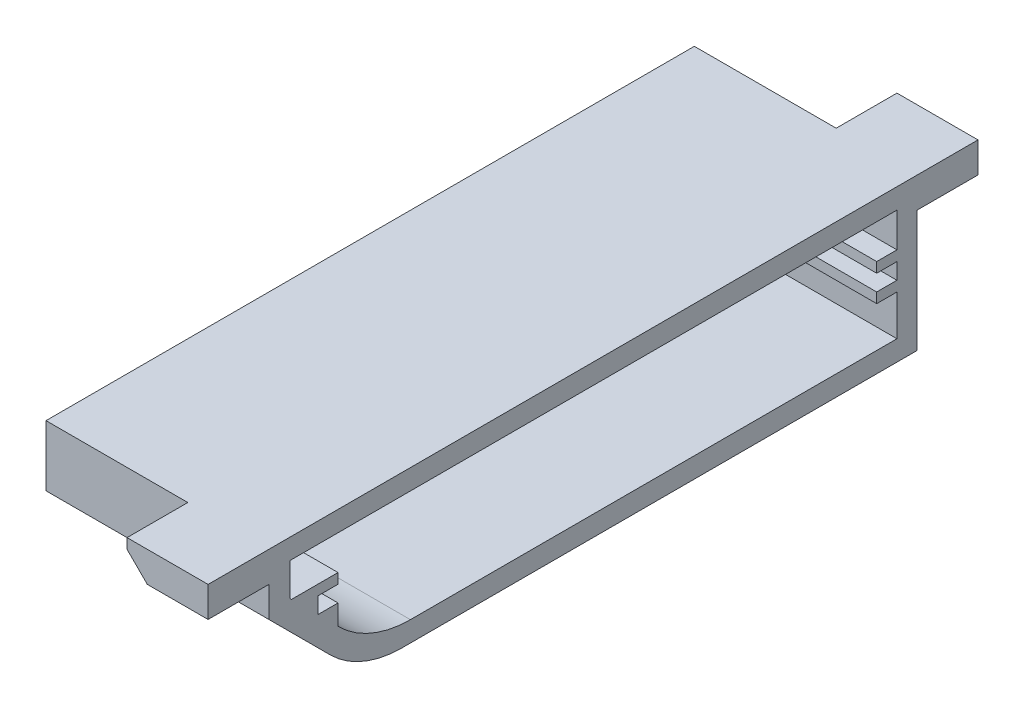
SolidWorks part; units mm, degrees
ref_plane "前视基准面" through (0, 0, 0) normal (0, 0, 1) x (1, 0, 0)
ref_plane "上视基准面" through (0, 0, 0) normal (0, 1, 0) x (1, 0, 0)
ref_plane "右视基准面" through (0, 0, 0) normal (1, 0, 0) x (0, 0, -1)
sketch "草图1" plane through (0, 0, 0) normal (0, 0, 1) x (1, 0, 0)
  line L0 (0, 0) -> (22, 0)
  line L1 (0, 0) -> (0, 15)
  line L2 (0, 15) -> (22, 15)
  line L3 (22, 15) -> (22, 0)
extrude "凸台-拉伸1" add sketch "草图1" along normal blind 2
sketch "草图2" plane through (0, 0, 0) normal (0, -1, 0) x (1, 0, 0)
  line L0 (0, 0) -> (0, 30)
  line L2 (22, 0) -> (22, 30)
  line L3 (22, 30) -> (0, 30)
  line L4 (0, 0) -> (22, 0)
extrude "凸台-拉伸2" add sketch "草图2" against normal blind 2
sketch "草图3" plane through (0, 0, 0) normal (-1, 0, 0) x (0, 0, 1)
  line L0 (0, 15) -> (64, 15)
  line L3 (0, 15) -> (0, 0) construction
  line L4 (0, 13) -> (0, 15)
  line L5 (64, 15) -> (64, 9)
  line L6 (64, 8) -> (64, 15) construction
  line L7 (30, 2) -> (53.4794, 2)
  line L8 (61.932, 10.4526) -> (61.932, 13)
  line L10 (30, 2) -> (30, 0)
  line L11 (61.932, 13) -> (0, 13)
  line L12 (30, 0) -> (55, 0)
  line L13 (64, 9) -> (55, 0)
  line L14 (60.9069, 8.7353) -> (60.9069, 8.7353)
  line L15 (60.9069, 8.7353) -> (60.9069, 8.7353)
  line L16 (60.9069, 8.7353) -> (60.9069, 8.7353)
  line L17 (60.9069, 8.7353) -> (60.9069, 8.7353)
  line L18 (60.9069, 8.7353) -> (60.9069, 8.7353)
  line L19 (60.9069, 8.7353) -> (55.1967, 3.0251)
  line L20 (55.1967, 3.0251) -> (55.1967, 3.0251)
  line L21 (55.1967, 3.0251) -> (55.1967, 3.0251)
  line L22 (55.1967, 3.0251) -> (55.1967, 3.0251)
  line L23 (60.9069, 8.7353) -> (61.932, 9.7604)
  line L24 (61.932, 9.7604) -> (61.932, 10.4526)
  line L25 (55.1967, 3.0251) -> (54.1716, 2)
  line L26 (54.1716, 2) -> (53.4794, 2)
  dimension "D1" = 2
extrude "凸台-拉伸3" add sketch "草图3" against normal blind 22
sketch "草图4" plane through (0, 0, 64) normal (0, 0, 1) x (1, 0, 0)
  line L1 (22, 15) -> (14, 15)
  line L2 (22, 15) -> (22, 12)
  line L3 (22, 12) -> (14, 12)
  line L4 (14, 15) -> (14, 12)
extrude "凸台-拉伸4" add sketch "草图4" along normal blind 6
sketch "草图5" plane through (0, 0, 0) normal (0, 0, -1) x (-1, 0, 0)
  line L1 (-22, 15) -> (-14, 15)
  line L2 (-22, 15) -> (-22, 12)
  line L3 (-22, 12) -> (-14, 12)
  line L4 (-14, 15) -> (-14, 12)
extrude "凸台-拉伸5" add sketch "草图5" along normal blind 6
chamfer "倒角1" distance 2 angle 45 2 edges at (14, 12, 67) (14, 12, -3)
sketch "草图6" plane through (0, 0, 0) normal (-1, 0, 0) x (0, 0, 1)
  line L0 (57.1716, 7) -> (59.1716, 7)
  line L1 (2, 13) -> (2, 2) construction
  line L2 (2, 6) -> (4, 6)
  line L3 (4, 6) -> (4, 7)
  line L4 (4, 7) -> (2, 7)
  line L5 (2, 9.6) -> (2, 8.6)
  line L6 (2, 8.6) -> (4, 8.6)
  line L7 (4, 8.6) -> (4, 9.6)
  line L8 (4, 9.6) -> (2, 9.6)
  line L9 (2, 7) -> (2, 6)
  line L10 (57.1716, 7) -> (57.1716, 5)
  line L11 (61.932, 9.7604) -> (54.1716, 2) construction
  line L19 (59.1716, 7) -> (59.1716, 8.6)
  line L20 (59.1716, 8.6) -> (57.1716, 8.6)
  line L21 (57.1716, 8.6) -> (57.1716, 9.6)
  line L22 (57.1716, 9.6) -> (61.7716, 9.6)
  line L25 (57.1716, 5) -> (59.1716, 5)
  line L26 (59.1716, 5) -> (59.1716, 6.3165)
  line L27 (59.1716, 6.3165) -> (60.5136, 6.3165)
  line L28 (60.5136, 6.3165) -> (60.5136, 7.9254)
  line L29 (60.5136, 7.9254) -> (61.7716, 7.9254)
  line L30 (61.7716, 7.9254) -> (61.7716, 9.6)
extrude "凸台-拉伸6" add sketch "草图6" against normal blind 22
fillet "圆角1" radius 10 2 edges at (11, 0, 55) (11, 2, 54.1716)
